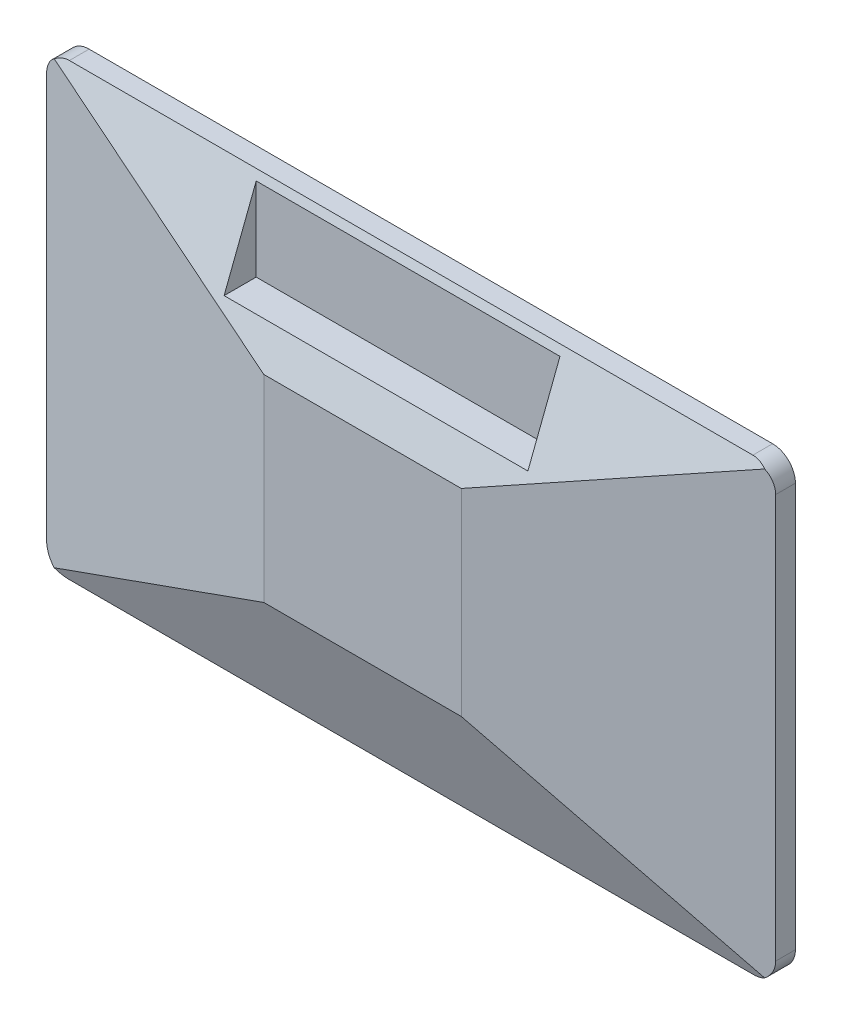
SolidWorks part; units mm, degrees
ref_plane "Front" through (0, 0, 0) normal (0, 0, 1) x (1, 0, 0)
ref_plane "Top" through (0, 0, 0) normal (0, 1, 0) x (1, 0, 0)
ref_plane "Right" through (0, 0, 0) normal (1, 0, 0) x (0, 0, -1)
sketch "Esquisse1" plane through (0, 0, 0) normal (0, 0, 1) x (1, 0, 0)
  line L1 (240, 148) -> (-240, 148)
  line L2 (240, 148) -> (240, -148)
  line L3 (240, -148) -> (-240, -148)
  line L4 (-240, 148) -> (-240, -148)
  line L5 (240, 148) -> (-240, -148) construction
  line L6 (240, -148) -> (-240, 148) construction
  point P0 (0, 0)
  dimension "D1" = 480
  dimension "D2" = 296
extrude "Boss.-Extru.1" add sketch "Esquisse1" along normal blind 13
ref_plane "Plan1" through (0, 0, 45) normal (0, 0, 1) x (1, 0, 0)
sketch "Esquisse2" plane through (0, 0, 45) normal (0, 0, 1) x (1, 0, 0)
  line L1 (-65, -65) -> (65, -65)
  line L2 (-65, -65) -> (-65, 65)
  line L3 (-65, 65) -> (65, 65)
  line L4 (65, -65) -> (65, 65)
  line L5 (-65, -65) -> (65, 65) construction
  line L6 (-65, 65) -> (65, -65) construction
  point P0 (0, 0)
  dimension "D1" = 130
  dimension "D2" = 130
loft "Lissage1" add profiles "Esquisse2" section "Esquisse2" section face at (0, 0, 13)
sketch "Esquisse3" plane through (0, 0, 0) normal (0, 0, -1) x (-1, 0, 0)
  line L0 (-240, 148) -> (240, 148) construction
  line L1 (230, -138) -> (-230, -138)
  line L2 (230, -138) -> (230, 138)
  line L3 (230, 138) -> (-230, 138)
  line L4 (-230, -138) -> (-230, 138)
  line L5 (230, -138) -> (-230, 138) construction
  line L6 (230, 138) -> (-230, -138) construction
  line L7 (-240, -148) -> (-240, 148) construction
  point P0 (0, 0)
  dimension "D1" = 10
  dimension "D2" = 10
extrude "Enlèv. mat.-Extru.1" cut sketch "Esquisse3" against normal blind 2
fillet "Congé1" radius 15 4 edges at (240, -148, 6.5) (-240, -148, 6.5) (-240, 148, 6.5) (240, 148, 6.5)
ref_plane "Plan2" through (0, 88, 0) normal (0, 1, 0) x (1, 0, 0)
sketch "Esquisse4" plane through (0, 88, 0) normal (0, 1, 0) x (1, 0, 0)
  line L0 (225, 0) -> (-225, 0) construction
  line L1 (100, -68.0297) -> (-100, -68.0297)
  line L2 (100, -68.0297) -> (100, -15)
  line L3 (100, -15) -> (-100, -15)
  line L4 (-100, -68.0297) -> (-100, -15)
  line L5 (100, -68.0297) -> (-100, -15) construction
  line L6 (100, -15) -> (-100, -68.0297) construction
  point P0 (0, -41.5148)
  dimension "D1" = 15
  dimension "D2" = 200
extrude "Enlèv. mat.-Extru.2" cut sketch "Esquisse4" along normal through all
sketch "Esquisse5" plane through (0, 0, 0) normal (0, 0, -1) x (-1, 0, 0)
  line L0 (-225, 148) -> (225, 148) construction
  line L1 (-200.6243, 141) -> (-215.6243, 141)
  line L2 (-200.6243, 141) -> (-200.6243, 146)
  line L3 (-200.6243, 146) -> (-215.6243, 146)
  line L4 (-215.6243, 141) -> (-215.6243, 146)
  line L5 (-200.6243, 141) -> (-215.6243, 146) construction
  line L6 (-200.6243, 146) -> (-215.6243, 141) construction
  line L7 (-177.6243, 141) -> (-192.6243, 141)
  line L8 (-177.6243, 141) -> (-177.6243, 146)
  line L9 (-177.6243, 146) -> (-192.6243, 146)
  line L10 (-192.6243, 141) -> (-192.6243, 146)
  line L11 (-177.6243, 141) -> (-192.6243, 146) construction
  line L12 (-177.6243, 146) -> (-192.6243, 141) construction
  line L13 (-154.6243, 141) -> (-169.6243, 141)
  line L14 (-154.6243, 141) -> (-154.6243, 146)
  line L15 (-154.6243, 146) -> (-169.6243, 146)
  line L16 (-169.6243, 141) -> (-169.6243, 146)
  line L17 (-154.6243, 141) -> (-169.6243, 146) construction
  line L18 (-154.6243, 146) -> (-169.6243, 141) construction
  point P0 (-208.1243, 143.5)
  point P5 (-185.1243, 143.5)
  point P10 (-162.1243, 143.5)
  dimension "D1" = 15
  dimension "D2" = 5
  dimension "D3" = 15
  dimension "D4" = 15
  dimension "D5" = 5
  dimension "D6" = 5
  dimension "D7" = 2
  dimension "D8" = 8
  dimension "D9" = 8
extrude "Boss.-Extru.2" add sketch "Esquisse5" along normal blind 1
equation "\"D3@Esquisse5\"=\"D1@Esquisse5\""
equation "\"D4@Esquisse5\"=\"D1@Esquisse5\""
equation "\"D5@Esquisse5\"=\"D2@Esquisse5\""
equation "\"D6@Esquisse5\"=\"D2@Esquisse5\""
